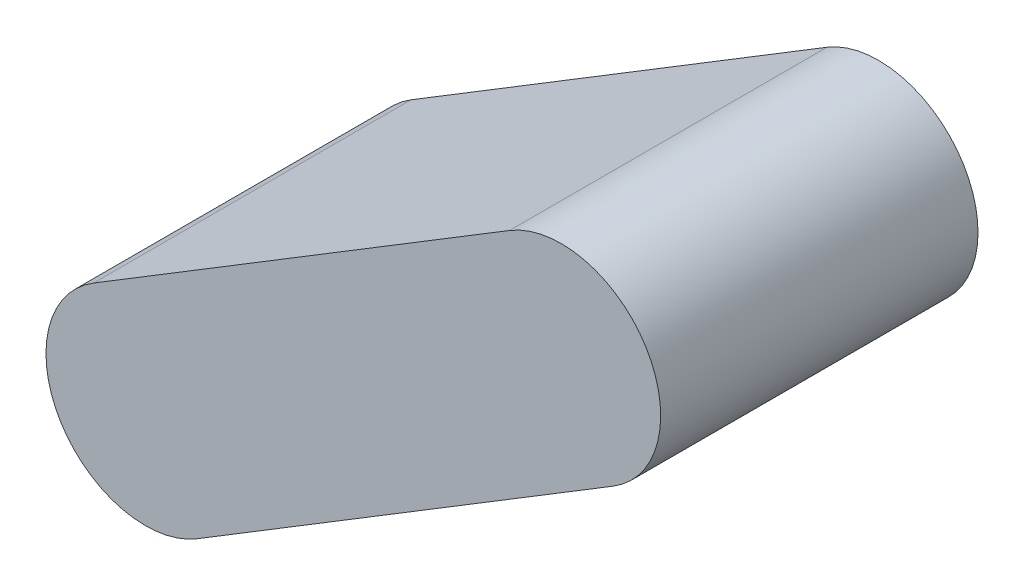
SolidWorks part; units mm, degrees
ref_plane "Front" through (0, 0, 0) normal (0, 0, 1) x (1, 0, 0)
ref_plane "Top" through (0, 0, 0) normal (0, 1, 0) x (1, 0, 0)
ref_plane "Right" through (0, 0, 0) normal (1, 0, 0) x (0, 0, -1)
sketch "Sketch1" plane through (0, 0, 0) normal (0, 0, 1) x (1, 0, 0)
  line L0 (-1161.0105, 337.7918) -> (-742.5908, 592.7918)
  line L1 (-638.5092, 422.0082) -> (-1056.9288, 167.0082)
  circle A0 centre (-690.55, 507.4) radius 100 construction
  arc A1 (-742.5908, 592.7918) -> (-638.5092, 422.0082) centre (-690.55, 507.4) cw
  arc A2 (-1161.0105, 337.7918) -> (-1056.9288, 167.0082) centre (-1108.9696, 252.4) ccw
  circle A3 centre (-1108.9696, 252.4) radius 100 construction
extrude "Boss-Extrude1" add sketch "Sketch1" along normal mid plane 319.278
equation "\"mass\"= \"human weight@FS2-FR-HA-A-0001-V1, HUMAN ANALOG.Assembly\" * \"torso percent@FS2-FR-HA-A-0001-V1, HUMAN ANALOG.Assembly\""
